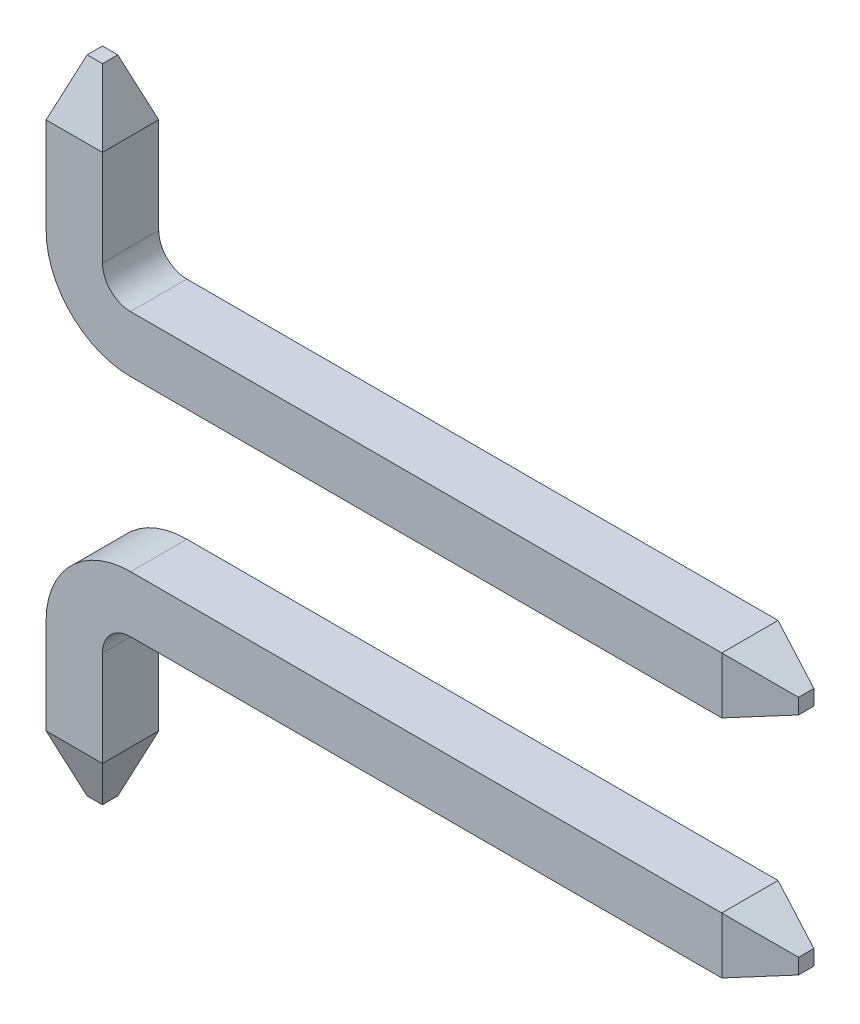
SolidWorks part; units mm, degrees
ref_plane "Front Plane" through (0, 0, 0) normal (0, 0, 1) x (1, 0, 0)
ref_plane "Top Plane" through (0, 0, 0) normal (0, 1, 0) x (1, 0, 0)
ref_plane "Right Plane" through (0, 0, 0) normal (1, 0, 0) x (0, 0, -1)
sketch "Sketch1" plane through (0, 0, 0) normal (0, 1, 0) x (1, 0, 0)
  line L1 (0, 0) -> (0.5, 0)
  line L2 (0, 0) -> (0, 0.5)
  line L3 (0, 0.5) -> (0.5, 0.5)
  line L4 (0.5, 0) -> (0.5, 0.5)
sketch "Sketch2" plane through (0, 0, 0) normal (0, 0, 1) x (1, 0, 0)
  line L0 (0, 0) -> (0.5, 0) construction
  line L1 (0.25, 0) -> (0.25, 1.35) construction
  line L2 (0.25, 1.35) -> (6, 1.35) construction
  line L3 (0.25, 0) -> (0.25, 0.85)
  line L4 (0.75, 1.35) -> (6, 1.35)
  line L5 (0.25, 0) -> (0.75, 0) construction
  line L6 (0.75, 0) -> (0.75, 1.35) construction
  line L7 (0.75, 0.85) -> (0.25, 0.85) construction
  arc A0 (0.25, 0.85) -> (0.75, 1.35) centre (0.75, 0.85) cw
sweep "Sweep4" add profiles "Sketch1" path "Sketch2"
sketch "Sketch6" plane through (6, 0, 0) normal (1, 0, 0) x (0, 0, -1)
  line L1 (0, 1.6) -> (0.5, 1.6)
  line L2 (0, 1.6) -> (0, 1.1)
  line L3 (0, 1.1) -> (0.5, 1.1)
  line L4 (0.5, 1.6) -> (0.5, 1.1)
extrude "Boss-Extrude1" add sketch "Sketch6" along normal blind 0.5 draft 20
sketch "Sketch7" plane through (0, 0, 0) normal (0, -1, 0) x (1, 0, 0)
  line L1 (0, 0) -> (0.5, 0)
  line L2 (0, 0) -> (0, -0.5)
  line L3 (0, -0.5) -> (0.5, -0.5)
  line L4 (0.5, 0) -> (0.5, -0.5)
extrude "Boss-Extrude2" add sketch "Sketch7" along normal blind 0.5 draft 20
ref_plane "Plane1" through (0, 2.35, 0) normal (0, 1, 0) x (-1, 0, 0)
mirror "Mirror3" about plane through (0, 2.35, 0) normal (0, 1, 0) of bodies 104
